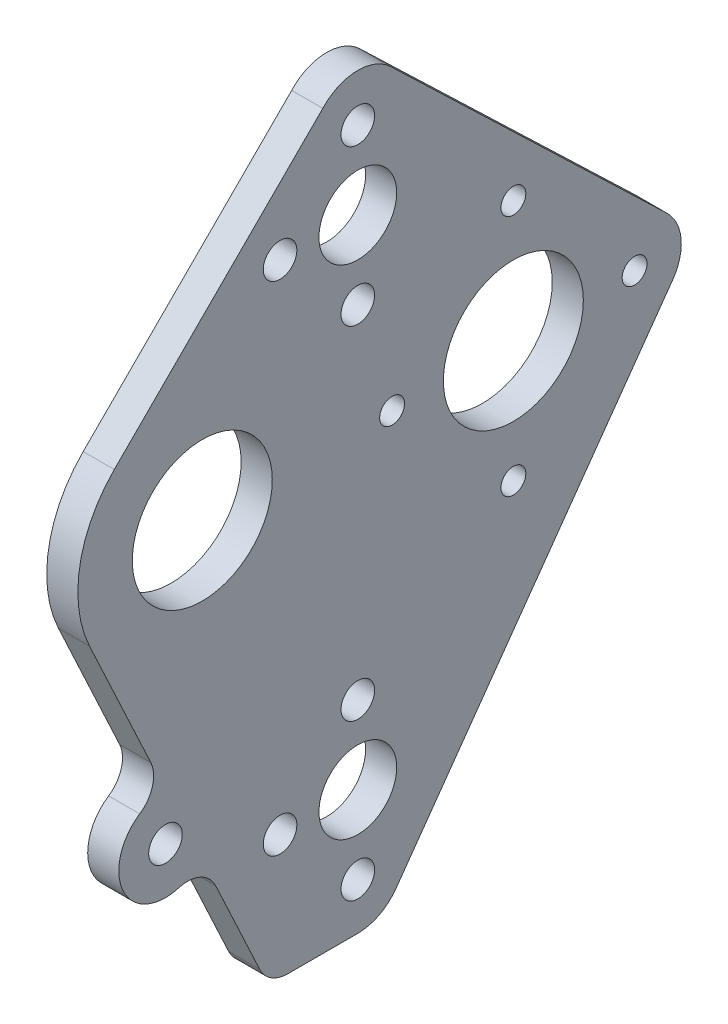
SolidWorks part; units mm, degrees
ref_plane "Front Plane" through (0, 0, 0) normal (0, 0, 1) x (1, 0, 0)
ref_plane "Top Plane" through (0, 0, 0) normal (0, 1, 0) x (1, 0, 0)
ref_plane "Right Plane" through (0, 0, 0) normal (1, 0, 0) x (0, 0, -1)
sketch "Sketch1" plane through (0, 0, 0) normal (1, 0, 0) x (0, 0, -1)
  line L0 (0, 55) -> (0, -55) construction
  line L1 (-19.05, 0) -> (-26.5619, -53.4497) construction
  line L2 (12.7, 38.1) -> (12.7, 53.975) construction
  line L3 (12.7, 38.1) -> (-3.175, 38.1) construction
  line L4 (12.7, -63.5) -> (-3.175, -63.5) construction
  line L5 (25.4, 55.2248) -> (25.4, -77.9586) construction
  line L6 (12.7, -88.9) -> (-1.5757, -88.9)
  line L9 (55, 0) -> (-55, 0) construction
  line L10 (-37.0105, 17.9605) -> (5.5449, 60.5159)
  line L11 (-42.0702, -10.7345) -> (-29.5744, -37.5319)
  line L12 (-16.3045, -65.9893) -> (-7.3307, -85.2336)
  line L13 (75.7966, 6.8732) -> (19.4115, 60.9704)
  line L14 (76.9621, -5.5237) -> (20.4598, -84.8987)
  circle A0 centre (-19.05, 0) radius 14.2875
  circle A1 centre (12.7, 38.1) radius 7.9375
  circle A2 centre (12.7, -63.5) radius 7.9375
  circle A3 centre (-26.5619, -53.4497) radius 3.429
  circle A4 centre (12.7, 38.1) radius 15.875 construction
  circle A6 centre (12.7, 53.975) radius 3.429
  circle A8 centre (12.7, -63.5) radius 15.875 construction
  circle A9 centre (-3.175, -63.5) radius 3.429
  circle A10 centre (12.7, -47.625) radius 3.429
  circle A12 centre (12.7, -79.375) radius 3.429
  circle A17 centre (-3.175, 38.1) radius 3.429
  circle A18 centre (12.7, 22.225) radius 3.429
  circle A19 centre (28.575, -63.5) radius 3.429 [skipped]
  arc A20 (-37.0105, 17.9605) -> (-42.0702, -10.7345) centre (-19.05, 0) ccw
  arc A21 (-31.8224, -45.5092) -> (-23.8605, -62.5836) centre (-26.5619, -53.4497) ccw
  arc A22 (-16.3045, -65.9893) -> (-23.8605, -62.5836) centre (-22.0596, -68.6729) ccw
  arc A23 (-31.8224, -45.5092) -> (-29.5744, -37.5319) centre (-35.3295, -40.2155) ccw
  arc A24 (-7.3307, -85.2336) -> (-1.5757, -88.9) centre (-1.5757, -82.55) ccw
  circle A26 centre (44.45, 0) radius 14.2875
  circle A27 centre (44.45, 0) radius 29.972 construction
  circle A28 centre (44.45, 0) radius 24.7523 construction
  circle A29 centre (44.45, 24.7523) radius 2.54
  circle A30 centre (69.2023, 0) radius 2.54
  circle A31 centre (44.45, -24.7523) radius 2.54
  circle A32 centre (19.6977, 0) radius 2.54
  arc A36 (12.7, -88.9) -> (20.4598, -84.8987) centre (12.7, -79.375) ccw
  arc A37 (19.4115, 60.9704) -> (5.5449, 60.5159) centre (12.7, 53.975) ccw
  arc A38 (76.9621, -5.5237) -> (75.7966, 6.8732) centre (69.2023, 0) ccw
  point P13 (73.3409, 9.2293)
  point P25 (0, 0)
  point P67 (44.45, 0)
  dimension "D1" = 15.875
  dimension "D2" = 28.575
  dimension "D6" = 6.858
  dimension "D8" = 31.75
  dimension "D12" = 4
  dimension "D18" = 19.05
  dimension "D19" = 6.858
  dimension "D15" = 45
  dimension "D23" = 50.8
  dimension "D25" = 6.35
  dimension "D26" = 63.5
  dimension "D27" = 59.944
  dimension "D28" = 49.5046
  dimension "D29" = 5.08
  dimension "D31" = 19.05
  dimension "D16" = 19.3886
  dimension "D3" = 38.1
  dimension "D4" = 63.5
  dimension "D5" = 53.975
  dimension "D7" = 8
  dimension "D10" = 90
  dimension "D11" = 15.875
  dimension "D13" = 15.875
  dimension "D14" = 25.4
  dimension "D17" = 88.9
  dimension "D20" = 12.7
  dimension "D21" = 12.7
  dimension "D22" = 19.05
  dimension "D24" = 65
  dimension "D9" = 3
  dimension "D30" = 4
extrude "Boss-Extrude1" add sketch "Sketch1" along normal blind 6.35
